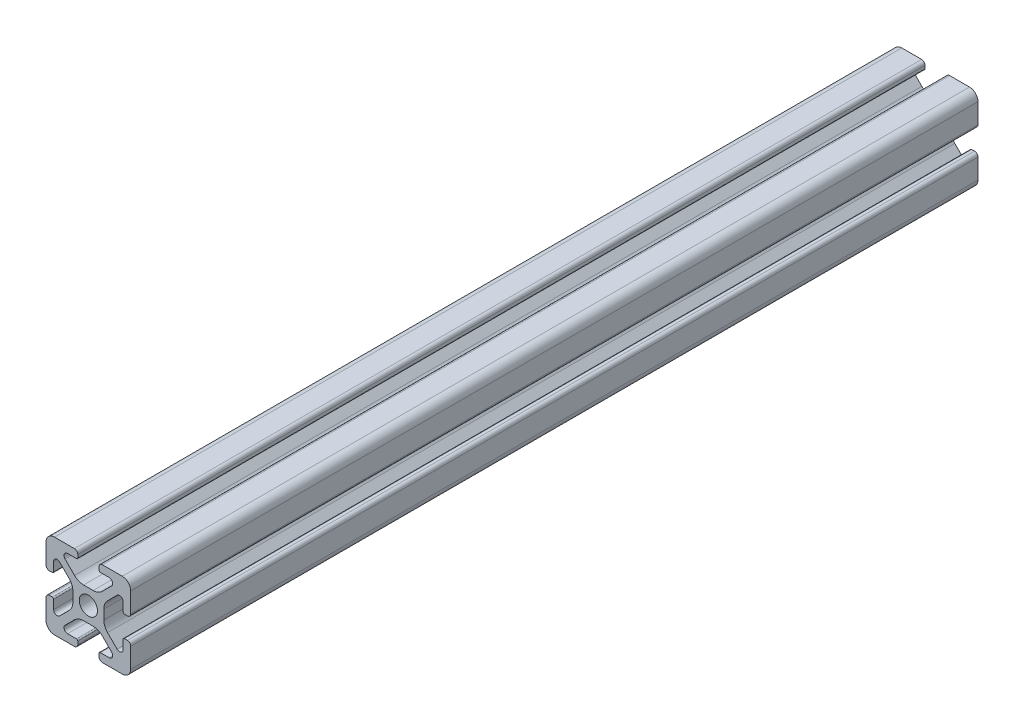
SolidWorks part; units mm, degrees
ref_plane "Front Plane" through (0, 0, 0) normal (0, 0, 1) x (1, 0, 0)
ref_plane "Top Plane" through (0, 0, 0) normal (0, 1, 0) x (1, 0, 0)
ref_plane "Right Plane" through (0, 0, 0) normal (1, 0, 0) x (0, 0, -1)
ref_plane "Plane1" through (0, 0, 0) normal (0, 0, -1) x (-1, 0, 0)
sketch "Sketch1" plane through (0, 0, 0) normal (0, 0, -1) x (-1, 0, 0)
  line L0 (-12.5, 0.8) -> (-12.5, 1.5)
  line L1 (-12.8, 1.8) -> (-14.9176, 1.8)
  line L2 (-15.5062, 3.221) -> (-13.2559, 5.4713)
  line L3 (-11.1346, 6.35) -> (-8.8654, 6.35)
  line L4 (-6.7441, 5.4713) -> (-4.4938, 3.221)
  line L5 (-5.0824, 1.8) -> (-7.2, 1.8)
  line L6 (-7.5, 1.5) -> (-7.5, 0.8)
  line L7 (-6.7, 0) -> (-2, 0)
  line L8 (0, 2) -> (0, 6.7)
  line L9 (-0.8, 7.5) -> (-1.5, 7.5)
  line L10 (-1.8, 7.2) -> (-1.8, 5.0824)
  line L11 (-3.221, 4.4938) -> (-5.4713, 6.7441)
  line L12 (-6.35, 8.8654) -> (-6.35, 11.1346)
  line L13 (-5.4713, 13.2559) -> (-3.221, 15.5062)
  line L14 (-1.8, 14.9176) -> (-1.8, 12.8)
  line L15 (-1.5, 12.5) -> (-0.8, 12.5)
  line L16 (0, 13.3) -> (0, 18)
  line L17 (-2, 20) -> (-6.7, 20)
  line L18 (-7.5, 19.2) -> (-7.5, 18.5)
  line L19 (-7.2, 18.2) -> (-5.0824, 18.2)
  line L20 (-4.4938, 16.779) -> (-6.7441, 14.5287)
  line L21 (-8.8654, 13.65) -> (-11.1346, 13.65)
  line L22 (-13.2559, 14.5287) -> (-15.5062, 16.779)
  line L23 (-14.9176, 18.2) -> (-12.8, 18.2)
  line L24 (-12.5, 18.5) -> (-12.5, 19.2)
  line L25 (-13.3, 20) -> (-18, 20)
  line L26 (-20, 18) -> (-20, 13.3)
  line L27 (-19.2, 12.5) -> (-18.5, 12.5)
  line L28 (-18.2, 12.8) -> (-18.2, 14.9176)
  line L29 (-16.779, 15.5062) -> (-14.5287, 13.2559)
  line L30 (-13.65, 11.1346) -> (-13.65, 8.8654)
  line L31 (-14.5287, 6.7441) -> (-16.779, 4.4938)
  line L32 (-18.2, 5.0824) -> (-18.2, 7.2)
  line L33 (-18.5, 7.5) -> (-19.2, 7.5)
  line L34 (-20, 6.7) -> (-20, 2)
  line L35 (-18, 0) -> (-13.3, 0)
  arc A0 (-12.5, 1.5) -> (-12.8, 1.8) centre (-12.8, 1.5) ccw
  arc A1 (-14.9176, 1.8) -> (-15.5062, 3.221) centre (-14.9176, 2.6324) cw
  arc A2 (-13.2559, 5.4713) -> (-11.1346, 6.35) centre (-11.1346, 3.35) cw
  arc A3 (-8.8654, 6.35) -> (-6.7441, 5.4713) centre (-8.8654, 3.35) cw
  arc A4 (-4.4938, 3.221) -> (-5.0824, 1.8) centre (-5.0824, 2.6324) cw
  arc A5 (-7.2, 1.8) -> (-7.5, 1.5) centre (-7.2, 1.5) ccw
  arc A6 (-7.5, 0.8) -> (-6.7, 0) centre (-6.7, 0.8) ccw
  arc A7 (-2, 0) -> (0, 2) centre (-2, 2) ccw
  arc A8 (0, 6.7) -> (-0.8, 7.5) centre (-0.8, 6.7) ccw
  arc A9 (-1.5, 7.5) -> (-1.8, 7.2) centre (-1.5, 7.2) ccw
  arc A10 (-1.8, 5.0824) -> (-3.221, 4.4938) centre (-2.6324, 5.0824) cw
  arc A11 (-5.4713, 6.7441) -> (-6.35, 8.8654) centre (-3.35, 8.8654) cw
  arc A12 (-6.35, 11.1346) -> (-5.4713, 13.2559) centre (-3.35, 11.1346) cw
  arc A13 (-3.221, 15.5062) -> (-1.8, 14.9176) centre (-2.6324, 14.9176) cw
  arc A14 (-1.8, 12.8) -> (-1.5, 12.5) centre (-1.5, 12.8) ccw
  arc A15 (-0.8, 12.5) -> (0, 13.3) centre (-0.8, 13.3) ccw
  arc A16 (0, 18) -> (-2, 20) centre (-2, 18) ccw
  arc A17 (-6.7, 20) -> (-7.5, 19.2) centre (-6.7, 19.2) ccw
  arc A18 (-7.5, 18.5) -> (-7.2, 18.2) centre (-7.2, 18.5) ccw
  arc A19 (-5.0824, 18.2) -> (-4.4938, 16.779) centre (-5.0824, 17.3676) cw
  arc A20 (-6.7441, 14.5287) -> (-8.8654, 13.65) centre (-8.8654, 16.65) cw
  arc A21 (-11.1346, 13.65) -> (-13.2559, 14.5287) centre (-11.1346, 16.65) cw
  arc A22 (-15.5062, 16.779) -> (-14.9176, 18.2) centre (-14.9176, 17.3676) cw
  arc A23 (-12.8, 18.2) -> (-12.5, 18.5) centre (-12.8, 18.5) ccw
  arc A24 (-12.5, 19.2) -> (-13.3, 20) centre (-13.3, 19.2) ccw
  arc A25 (-18, 20) -> (-20, 18) centre (-18, 18) ccw
  arc A26 (-20, 13.3) -> (-19.2, 12.5) centre (-19.2, 13.3) ccw
  arc A27 (-18.5, 12.5) -> (-18.2, 12.8) centre (-18.5, 12.8) ccw
  arc A28 (-18.2, 14.9176) -> (-16.779, 15.5062) centre (-17.3676, 14.9176) cw
  arc A29 (-14.5287, 13.2559) -> (-13.65, 11.1346) centre (-16.65, 11.1346) cw
  arc A30 (-13.65, 8.8654) -> (-14.5287, 6.7441) centre (-16.65, 8.8654) cw
  arc A31 (-16.779, 4.4938) -> (-18.2, 5.0824) centre (-17.3676, 5.0824) cw
  arc A32 (-18.2, 7.2) -> (-18.5, 7.5) centre (-18.5, 7.2) ccw
  arc A33 (-19.2, 7.5) -> (-20, 6.7) centre (-19.2, 6.7) ccw
  arc A34 (-20, 2) -> (-18, 0) centre (-18, 2) ccw
  arc A35 (-13.3, 0) -> (-12.5, 0.8) centre (-13.3, 0.8) ccw
  circle A36 centre (-10, 10) radius 2.15
extrude "Boss-Extrude1" add sketch "Sketch1" against normal blind 200
equation "\"plate_thickness\" = 6.35 'thickness of the plate "
equation "\"t_height\" = 200"
equation "\"t_width\" = 240"
equation "\"t_length\" = 240"
equation "\"D1@Boss-Extrude1\"=\"t_height\""
